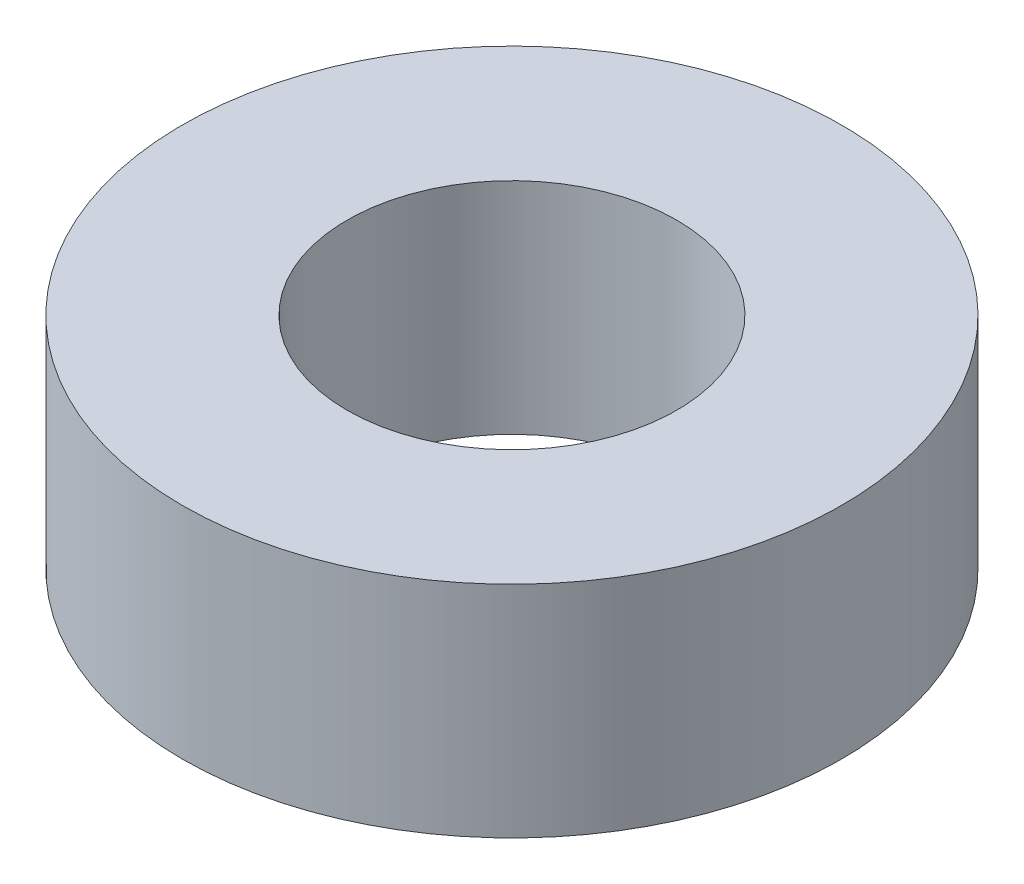
SolidWorks part; units mm, degrees
ref_plane "Front Plane" through (0, 0, 0) normal (0, 0, 1) x (1, 0, 0)
ref_plane "Top Plane" through (0, 0, 0) normal (0, 1, 0) x (1, 0, 0)
ref_plane "Right Plane" through (0, 0, 0) normal (1, 0, 0) x (0, 0, -1)
sketch "Sketch1" plane through (0, 0, 0) normal (0, 1, 0) x (1, 0, 0)
  circle A0 centre (0, 0) radius 3
  circle A1 centre (0, 0) radius 6
  dimension "D1" = 6
  dimension "D2" = 12
extrude "Boss-Extrude1" add sketch "Sketch1" along normal blind 4
